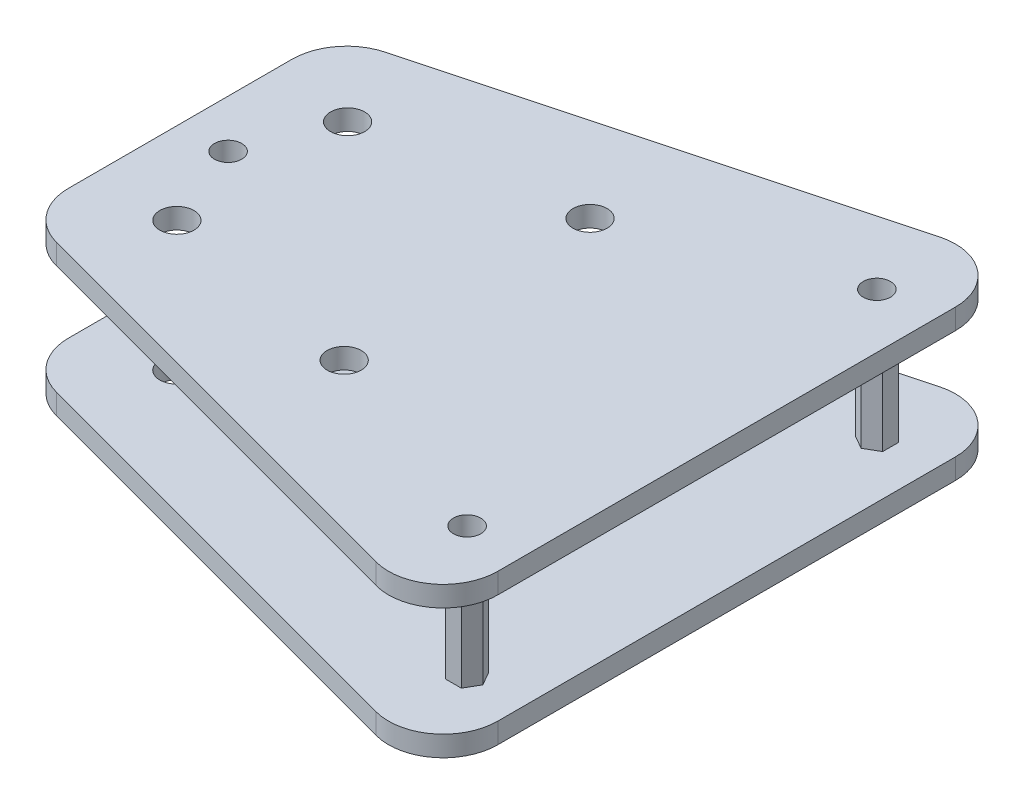
SolidWorks part; units mm, degrees
ref_plane "Alzado" through (0, 0, 0) normal (0, 0, 1) x (1, 0, 0)
ref_plane "Planta" through (0, 0, 0) normal (0, 1, 0) x (1, 0, 0)
ref_plane "Vista lateral" through (0, 0, 0) normal (1, 0, 0) x (0, 0, -1)
sketch "Croquis1" plane through (0, 0, 0) normal (0, 1, 0) x (1, 0, 0)
  line L0 (0, 16.3614) -> (0, -16.3614)
  line L1 (5.9294, -24.0888) -> (69.9294, -41.2375)
  line L2 (80, -33.5101) -> (80, 33.5101)
  line L3 (69.9294, 41.2375) -> (5.9294, 24.0888)
  line L4 (0, 0) -> (80, 0) construction
  line L5 (12, 12.5) -> (12, -12.5) construction
  line L6 (42, 18) -> (42, -18) construction
  line L7 (72, 30) -> (72, -30) construction
  circle A0 centre (12, 12.5) radius 2.5
  circle A1 centre (12, -12.5) radius 2.5
  circle A2 centre (42, 18) radius 2.5
  circle A3 centre (42, -18) radius 2.5
  arc A4 (80, 33.5101) -> (69.9294, 41.2375) centre (72, 33.5101) ccw
  arc A5 (69.9294, -41.2375) -> (80, -33.5101) centre (72, -33.5101) ccw
  arc A6 (0, -16.3614) -> (5.9294, -24.0888) centre (8, -16.3614) ccw
  arc A7 (0, 16.3614) -> (5.9294, 24.0888) centre (8, 16.3614) cw
  circle A8 centre (7, 0) radius 2
  circle A9 centre (72, -30) radius 2
  circle A10 centre (72, 30) radius 2
  point P3 (80, 0)
  point P10 (12, 0)
  point P15 (42, 0)
  point P18 (40, 0)
  point P25 (0, -22.5)
  point P28 (0, 22.5)
  point P35 (72, 0)
  dimension "D2" = 5
  dimension "D9" = 8
  dimension "D11" = 4
  dimension "D1" = 25
  dimension "D3" = 30
  dimension "D4" = 36
  dimension "D5" = 45
  dimension "D6" = 80
  dimension "D7" = 28
  dimension "D8" = 75
  dimension "D10" = 5
  dimension "D12" = 30
  dimension "D13" = 60
extrude "Saliente-Extruir1" add sketch "Croquis1" along normal blind 22
sketch "Croquis2" plane through (0, 0, 0) normal (0, 0, 1) x (1, 0, 0)
  line L0 (0, 22) -> (0, 0) construction
  line L1 (0, 19) -> (80, 19)
  line L2 (0, 19) -> (0, 3)
  line L3 (0, 3) -> (80, 3)
  line L4 (80, 19) -> (80, 3)
  line L5 (80, 22) -> (80, 0) construction
  point P8 (0, 11)
  dimension "D1" = 16
extrude "Cortar-Extruir1" cut sketch "Croquis2" against normal mid plane 100
sketch "Croquis3" plane through (0, 3, 0) normal (0, 1, 0) x (1, 0, 0)
  line L1 (7, -2.3094) -> (9, -1.1547)
  line L2 (9, -1.1547) -> (9, 1.1547)
  line L3 (9, 1.1547) -> (7, 2.3094)
  line L4 (7, 2.3094) -> (5, 1.1547)
  line L5 (5, 1.1547) -> (5, -1.1547)
  line L6 (5, -1.1547) -> (7, -2.3094)
  line L7 (70.8453, -32) -> (73.1547, -32)
  line L8 (73.1547, -32) -> (74.3094, -30)
  line L9 (74.3094, -30) -> (73.1547, -28)
  line L10 (73.1547, -28) -> (70.8453, -28)
  line L11 (70.8453, -28) -> (69.6906, -30)
  line L12 (69.6906, -30) -> (70.8453, -32)
  line L13 (74, 28.8453) -> (74, 31.1547)
  line L14 (74, 31.1547) -> (72, 32.3094)
  line L15 (72, 32.3094) -> (70, 31.1547)
  line L16 (70, 31.1547) -> (70, 28.8453)
  line L17 (70, 28.8453) -> (72, 27.6906)
  line L18 (72, 27.6906) -> (74, 28.8453)
  circle A0 centre (7, 0) radius 2 construction
  circle A1 centre (72, -30) radius 2 construction
  circle A2 centre (72, 30) radius 2 construction
  circle A3 centre (72, 30) radius 2 construction
  circle A4 centre (72, -30) radius 2 construction
  circle A5 centre (7, 0) radius 2 construction
extrude "Saliente-Extruir2" add sketch "Croquis3" along normal blind 16 separate body
